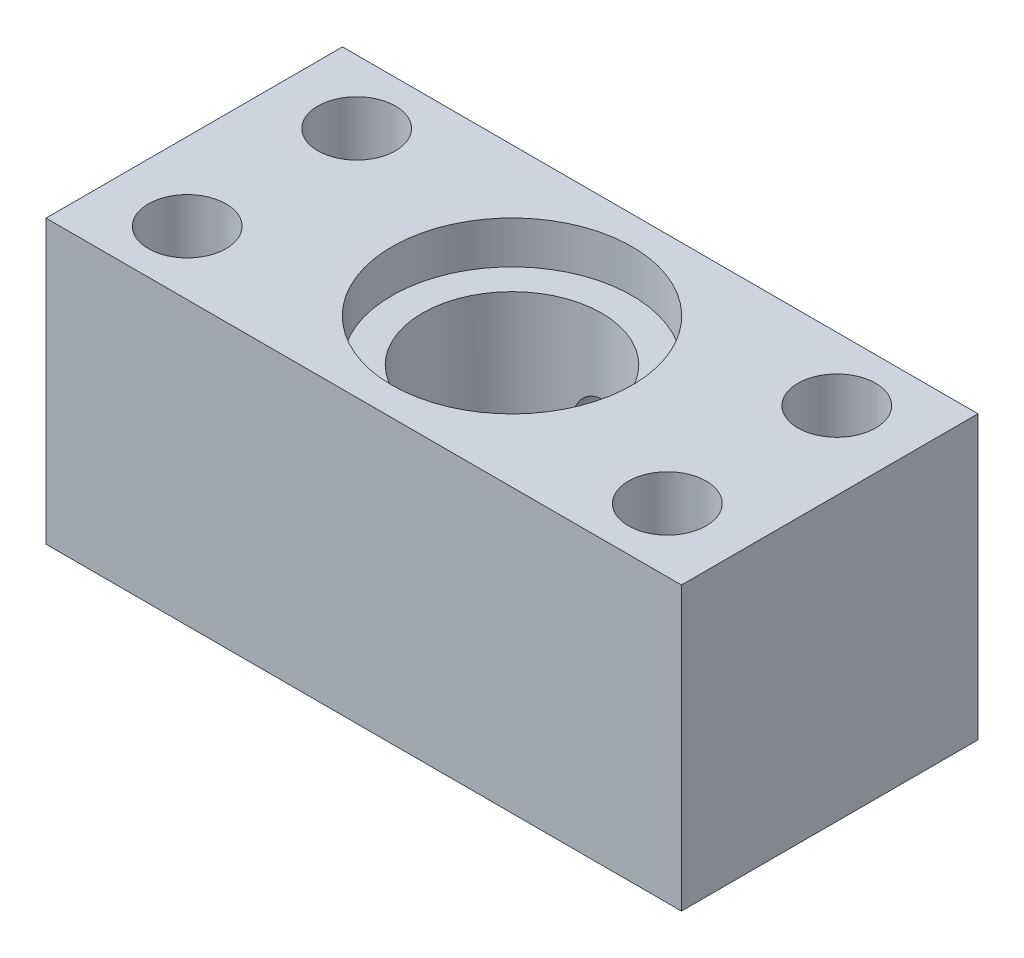
SolidWorks part; units mm, degrees
ref_plane "Front Plane" through (0, 0, 0) normal (0, 0, 1) x (1, 0, 0)
ref_plane "Top Plane" through (0, 0, 0) normal (0, 1, 0) x (1, 0, 0)
ref_plane "Right Plane" through (0, 0, 0) normal (1, 0, 0) x (0, 0, -1)
sketch "Sketch1" plane through (0, 0, 0) normal (0, 1, 0) x (1, 0, 0)
  line L1 (0, 0) -> (45, 0)
  line L2 (0, 0) -> (0, 21)
  line L3 (0, 21) -> (45, 21)
  line L4 (45, 0) -> (45, 21)
  dimension "D1" = 45
  dimension "D2" = 21
extrude "Boss-Extrude1" add sketch "Sketch1" along normal blind 20
sketch "Sketch2" plane through (0, 0, 0) normal (0, -1, 0) x (1, 0, 0)
  line L0 (45, 0) -> (45, -21) construction
  line L1 (45, -21) -> (0, -21) construction
  line L2 (0, 0) -> (45, 0) construction
  line L3 (22.5, -21) -> (22.5, 0) construction
  line L4 (45, -10.5) -> (0, -10.5) construction
  line L5 (0, -21) -> (0, 0) construction
  circle A0 centre (39.5, -16.5) radius 2.75
  circle A1 centre (39.5, -4.5) radius 2.75
  circle A2 centre (5.5, -16.5) radius 2.75
  circle A3 centre (5.5, -4.5) radius 2.75
  point P4 (45, -10.5)
  point P7 (22.5, -21)
  dimension "D1" = 6
  dimension "D3" = 6
  dimension "D5" = 17
  dimension "D7" = 6
  dimension "D9" = 5.5
  dimension "D10" = 5.5
  dimension "D11" = 5.5
  dimension "D12" = 5.5
  dimension "D2" = 17
  dimension "D4" = 17
  dimension "D6" = 6
  dimension "D8" = 17
extrude "AlignmentHoles" cut sketch "Sketch2" against normal through all
sketch "Sketch3" plane through (0, 0, 0) normal (0, -1, 0) x (1, 0, 0)
  line L0 (22.5, -21) -> (22.5, 0) construction
  line L1 (45, -21) -> (0, -21) construction
  line L2 (0, 0) -> (45, 0) construction
  line L3 (45, 0) -> (45, -21) construction
  line L4 (45, -10.5) -> (0, -10.5) construction
  line L5 (0, -21) -> (0, 0) construction
  circle A0 centre (22.5, -10.5) radius 6.4897
  dimension "D1" = 0
  dimension "D2" = 0
sketch "Sketch4" plane through (0, 20, 0) normal (0, 1, 0) x (1, 0, 0)
  line L0 (22.5, 0) -> (22.5, 21) construction
  line L1 (0, 0) -> (45, 0) construction
  line L2 (45, 21) -> (0, 21) construction
  line L3 (0, 10.5) -> (45, 10.5) construction
  line L4 (0, 21) -> (0, 0) construction
  line L5 (45, 0) -> (45, 21) construction
  circle A0 centre (22.5, 10.5) radius 8.5
  dimension "D1" = 17
extrude "PiezoCut" cut sketch "Sketch4" against normal blind 3
hole_wizard "0.535-40 Tapped Hole1" positions "Sketch7" profile "Sketch8" tap size "0.535-40" standard "Thorlabs" end condition through all
sketch "Sketch7" plane through (0, 0, 0) normal (0, -1, 0) x (-1, 0, 0)
  point P0 (-22.5, 10.5)
sketch "Sketch8" plane through (22.5, 0, -10.5) normal (1, 0, 0) x (0, 0, -1)
  line L0 (0, 0) -> (0, 20)
  line L1 (0, 20) -> (6.35, 20)
  line L2 (6.35, 20) -> (6.35, 0)
  line L5 (6.35, 0) -> (0, 0)
  line L11 (0, -6.35) -> (0, 107.95) construction
  dimension "Thru Tap Drill Dia." = 12.7
  dimension "Thru Tap Drill Depth" = 20
cosmetic thread "Hole Thread2" parameters "D2"=13.589
hole_wizard "#8-32 Tapped Hole2" positions "Sketch6" profile "Sketch5" tap size "#8-32" standard "ANSI Inch"
sketch "Sketch6" plane through (0, 0, -21) normal (0, 0, -1) x (-1, 0, 0)
  line L0 (-45, 0) -> (0, 0) construction
  line L4 (-22.5, 0) -> (-22.5, 20) construction
  line L5 (-45, 20) -> (0, 20) construction
  line L6 (-45, 10) -> (0, 10) construction
  line L7 (-45, 20) -> (-45, 0) construction
  line L8 (0, 20) -> (0, 0) construction
  point P0 (-22.5, 10)
  dimension "D1" = 0
  dimension "D2" = 0
sketch "Sketch5" plane through (22.5, 10, -21) normal (1, 0, 0) x (0, 1, 0)
  line L0 (0, 0) -> (0, 11.0378)
  line L1 (0, 11.0378) -> (1.7272, 10)
  line L2 (1.7272, 10) -> (1.7272, 0)
  line L5 (1.7272, 0) -> (0, 0)
  line L10 (0, 11.0378) -> (-1.7272, 10) construction
  line L11 (0, -6.35) -> (0, 107.95) construction
  dimension "Tap Drill Dia." = 3.4544
  dimension "Tap Drill Depth" = 10
  dimension "Drill Angle" = 118
cosmetic thread "Hole Thread3" parameters "D1"=4.3894, "D2"=4.1656
